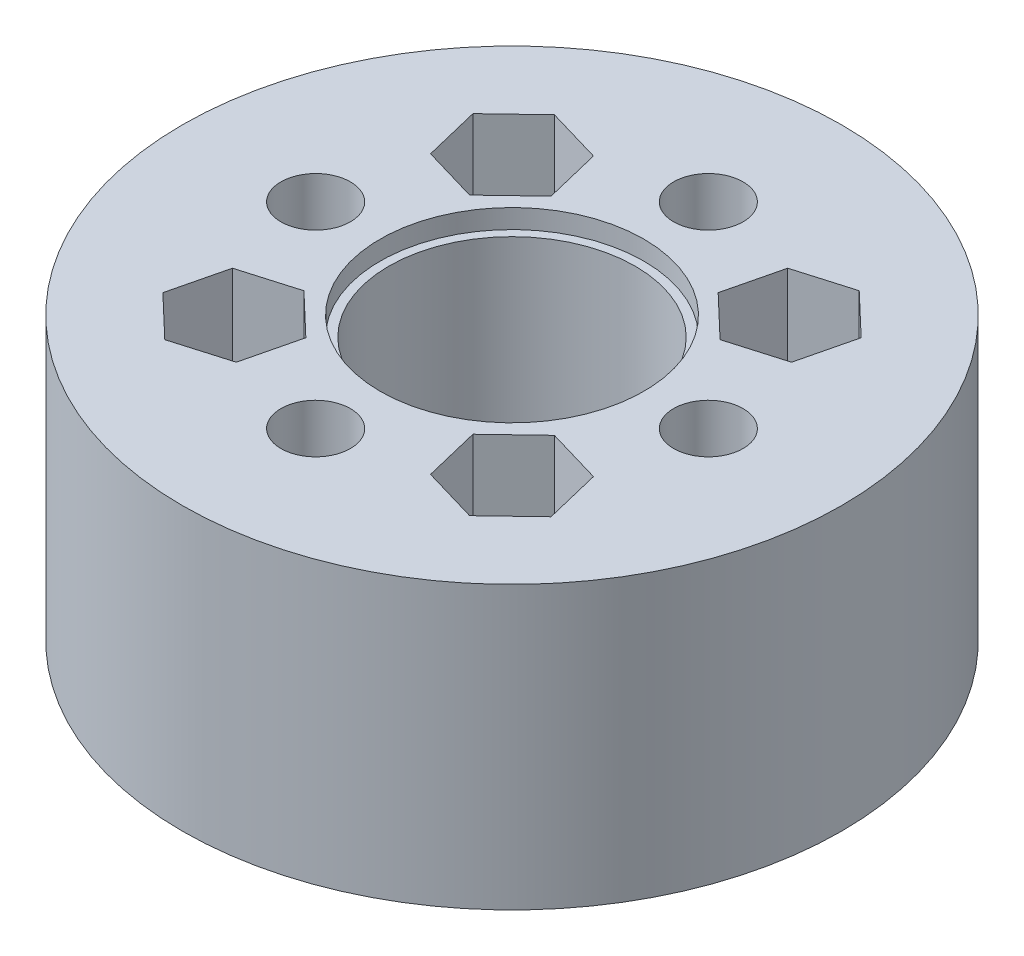
SolidWorks part; units mm, degrees
ref_plane "Front Plane" through (0, 0, 0) normal (0, 0, 1) x (1, 0, 0)
ref_plane "Top Plane" through (0, 0, 0) normal (0, 1, 0) x (1, 0, 0)
ref_plane "Right Plane" through (0, 0, 0) normal (1, 0, 0) x (0, 0, -1)
sketch "Sketch1" plane through (0, 0, 0) normal (0, 1, 0) x (1, 0, 0)
  line L0 (0, 11.315) -> (0, -11.315) construction
  line L1 (-8, 8) -> (8, 8) construction
  line L2 (-8, 8) -> (-8, -8) construction
  line L3 (-8, -8) -> (8, -8) construction
  line L4 (8, 8) -> (8, -8) construction
  line L5 (-8, 8) -> (8, -8) construction
  line L6 (-8, -8) -> (8, 8) construction
  line L7 (-11.315, 0) -> (11.315, 0) construction
  circle A0 centre (0, 0) radius 19
  circle A1 centre (-8, 8) radius 2.1
  circle A2 centre (-8, -8) radius 2.1
  circle A3 centre (8, 8) radius 2.1
  circle A4 centre (8, -8) radius 2.1
  circle A5 centre (0, 0) radius 7.1
  circle A6 centre (0, 11.315) radius 2
  circle A7 centre (11.315, 0) radius 2
  circle A8 centre (0, -11.315) radius 2
  circle A9 centre (-11.315, 0) radius 2
  point P15 (0, 0)
  point P18 (0, 0)
  dimension "40" = 38
  dimension "D4" = 4.2
  dimension "D5" = 14.2
  dimension "D8" = 4
  dimension "D2" = 16
  dimension "D3" = 16
  dimension "D6" = 22.63
  dimension "D7" = 22.63
extrude "Boss-Extrude1" add sketch "Sketch1" along normal blind 16.25
sketch "Sketch2" plane through (0, 16.25, 0) normal (0, 1, 0) x (1, 0, 0)
  circle A0 centre (0, 0) radius 7.6
  dimension "D1" = 15.2
extrude "Cut-Extrude1" cut sketch "Sketch2" against normal blind 1.1
sketch "Sketch3" plane through (0, 0, 0) normal (0, -1, 0) x (1, 0, 0)
  circle A0 centre (0, 0) radius 7.75
  dimension "D1" = 15.5
extrude "Cut-Extrude2" cut sketch "Sketch3" against normal blind 1.05
sketch "Sketch4" plane through (0, 16.25, 0) normal (0, 1, 0) x (1, 0, 0)
  line L0 (0, 0) -> (0, 4.7739) construction
  line L1 (-7.2168, 4.7739) -> (-4.8146, 7.0652)
  line L2 (-4.8146, 7.0652) -> (-5.5977, 10.2913)
  line L3 (-5.5977, 10.2913) -> (-8.7832, 11.2261)
  line L4 (-8.7832, 11.2261) -> (-11.1854, 8.9348)
  line L5 (-11.1854, 8.9348) -> (-10.4023, 5.7087)
  line L6 (-10.4023, 5.7087) -> (-7.2168, 4.7739)
  line L7 (0, 0) -> (2.7211, 0) construction
  line L8 (-10.4023, -5.7087) -> (-7.2168, -4.7739)
  line L9 (-11.1854, -8.9348) -> (-10.4023, -5.7087)
  line L10 (-8.7832, -11.2261) -> (-11.1854, -8.9348)
  line L11 (-5.5977, -10.2913) -> (-8.7832, -11.2261)
  line L12 (-4.8146, -7.0652) -> (-5.5977, -10.2913)
  line L13 (-7.2168, -4.7739) -> (-4.8146, -7.0652)
  line L14 (-7.2168, 4.7739) -> (-4.8146, 7.0652)
  line L15 (-4.8146, 7.0652) -> (-5.5977, 10.2913)
  line L16 (-5.5977, 10.2913) -> (-8.7832, 11.2261)
  line L17 (-8.7832, 11.2261) -> (-11.1854, 8.9348)
  line L18 (-11.1854, 8.9348) -> (-10.4023, 5.7087)
  line L19 (-10.4023, 5.7087) -> (-7.2168, 4.7739)
  line L20 (-10.4023, -5.7087) -> (-7.2168, -4.7739)
  line L21 (-11.1854, -8.9348) -> (-10.4023, -5.7087)
  line L22 (-8.7832, -11.2261) -> (-11.1854, -8.9348)
  line L23 (-5.5977, -10.2913) -> (-8.7832, -11.2261)
  line L24 (-4.8146, -7.0652) -> (-5.5977, -10.2913)
  line L25 (-7.2168, -4.7739) -> (-4.8146, -7.0652)
  line L26 (-7.2168, 4.7739) -> (-4.8146, 7.0652)
  line L27 (-4.8146, 7.0652) -> (-5.5977, 10.2913)
  line L28 (-5.5977, 10.2913) -> (-8.7832, 11.2261)
  line L29 (-8.7832, 11.2261) -> (-11.1854, 8.9348)
  line L30 (-11.1854, 8.9348) -> (-10.4023, 5.7087)
  line L31 (-10.4023, 5.7087) -> (-7.2168, 4.7739)
  line L32 (-10.4023, -5.7087) -> (-7.2168, -4.7739)
  line L33 (-11.1854, -8.9348) -> (-10.4023, -5.7087)
  line L34 (-8.7832, -11.2261) -> (-11.1854, -8.9348)
  line L35 (-5.5977, -10.2913) -> (-8.7832, -11.2261)
  line L36 (-4.8146, -7.0652) -> (-5.5977, -10.2913)
  line L37 (-7.2168, -4.7739) -> (-4.8146, -7.0652)
  line L38 (-7.2168, 4.7739) -> (-4.8146, 7.0652)
  line L39 (-4.8146, 7.0652) -> (-5.5977, 10.2913)
  line L40 (-5.5977, 10.2913) -> (-8.7832, 11.2261)
  line L41 (-8.7832, 11.2261) -> (-11.1854, 8.9348)
  line L42 (-11.1854, 8.9348) -> (-10.4023, 5.7087)
  line L43 (-10.4023, 5.7087) -> (-7.2168, 4.7739)
  line L44 (-10.4023, -5.7087) -> (-7.2168, -4.7739)
  line L45 (-11.1854, -8.9348) -> (-10.4023, -5.7087)
  line L46 (-8.7832, -11.2261) -> (-11.1854, -8.9348)
  line L47 (-5.5977, -10.2913) -> (-8.7832, -11.2261)
  line L48 (-4.8146, -7.0652) -> (-5.5977, -10.2913)
  line L49 (-7.2168, -4.7739) -> (-4.8146, -7.0652)
  line L50 (7.2168, -4.7739) -> (4.8146, -7.0652)
  line L51 (4.8146, -7.0652) -> (5.5977, -10.2913)
  line L52 (5.5977, -10.2913) -> (8.7832, -11.2261)
  line L53 (8.7832, -11.2261) -> (11.1854, -8.9348)
  line L54 (11.1854, -8.9348) -> (10.4023, -5.7087)
  line L55 (10.4023, -5.7087) -> (7.2168, -4.7739)
  line L56 (10.4023, 5.7087) -> (7.2168, 4.7739)
  line L57 (11.1854, 8.9348) -> (10.4023, 5.7087)
  line L58 (8.7832, 11.2261) -> (11.1854, 8.9348)
  line L59 (5.5977, 10.2913) -> (8.7832, 11.2261)
  line L60 (4.8146, 7.0652) -> (5.5977, 10.2913)
  line L61 (7.2168, 4.7739) -> (4.8146, 7.0652)
  line L62 (7.2168, -4.7739) -> (4.8146, -7.0652)
  line L63 (4.8146, -7.0652) -> (5.5977, -10.2913)
  line L64 (5.5977, -10.2913) -> (8.7832, -11.2261)
  line L65 (8.7832, -11.2261) -> (11.1854, -8.9348)
  line L66 (11.1854, -8.9348) -> (10.4023, -5.7087)
  line L67 (10.4023, -5.7087) -> (7.2168, -4.7739)
  line L68 (10.4023, 5.7087) -> (7.2168, 4.7739)
  line L69 (11.1854, 8.9348) -> (10.4023, 5.7087)
  line L70 (8.7832, 11.2261) -> (11.1854, 8.9348)
  line L71 (5.5977, 10.2913) -> (8.7832, 11.2261)
  line L72 (4.8146, 7.0652) -> (5.5977, 10.2913)
  line L73 (7.2168, 4.7739) -> (4.8146, 7.0652)
  line L74 (7.2168, -4.7739) -> (4.8146, -7.0652)
  line L75 (4.8146, -7.0652) -> (5.5977, -10.2913)
  line L76 (5.5977, -10.2913) -> (8.7832, -11.2261)
  line L77 (8.7832, -11.2261) -> (11.1854, -8.9348)
  line L78 (11.1854, -8.9348) -> (10.4023, -5.7087)
  line L79 (10.4023, -5.7087) -> (7.2168, -4.7739)
  line L80 (10.4023, 5.7087) -> (7.2168, 4.7739)
  line L81 (11.1854, 8.9348) -> (10.4023, 5.7087)
  line L82 (8.7832, 11.2261) -> (11.1854, 8.9348)
  line L83 (5.5977, 10.2913) -> (8.7832, 11.2261)
  line L84 (4.8146, 7.0652) -> (5.5977, 10.2913)
  line L85 (7.2168, 4.7739) -> (4.8146, 7.0652)
  line L86 (7.2168, -4.7739) -> (4.8146, -7.0652)
  line L87 (4.8146, -7.0652) -> (5.5977, -10.2913)
  line L88 (5.5977, -10.2913) -> (8.7832, -11.2261)
  line L89 (8.7832, -11.2261) -> (11.1854, -8.9348)
  line L90 (11.1854, -8.9348) -> (10.4023, -5.7087)
  line L91 (10.4023, -5.7087) -> (7.2168, -4.7739)
  line L92 (10.4023, 5.7087) -> (7.2168, 4.7739)
  line L93 (11.1854, 8.9348) -> (10.4023, 5.7087)
  line L94 (8.7832, 11.2261) -> (11.1854, 8.9348)
  line L95 (5.5977, 10.2913) -> (8.7832, 11.2261)
  line L96 (4.8146, 7.0652) -> (5.5977, 10.2913)
  line L97 (7.2168, 4.7739) -> (4.8146, 7.0652)
  circle A4 centre (-8, 8) radius 2.875 construction
  circle A5 centre (-8, -8) radius 2.875 construction
  circle A6 centre (-8, 8) radius 2.875 construction
  circle A7 centre (-8, -8) radius 2.875 construction
  circle A8 centre (-8, 8) radius 2.875 construction
  circle A9 centre (-8, -8) radius 2.875 construction
  circle A10 centre (-8, 8) radius 2.875 construction
  circle A11 centre (-8, -8) radius 2.875 construction
  circle A12 centre (8, -8) radius 2.875 construction
  circle A13 centre (8, 8) radius 2.875 construction
  circle A14 centre (8, -8) radius 2.875 construction
  circle A15 centre (8, 8) radius 2.875 construction
  circle A16 centre (8, -8) radius 2.875 construction
  circle A17 centre (8, 8) radius 2.875 construction
  circle A18 centre (8, -8) radius 2.875 construction
  circle A19 centre (8, 8) radius 2.875 construction
  circle M7 centre (8, -8) radius 2.1
  circle M8 centre (-8, -8) radius 2.1
  circle M10 centre (-8, 8) radius 2.1
  circle M11 centre (8, 8) radius 2.1
  dimension "D1" = 5.75
extrude "Cut-Extrude3" cut sketch "Sketch4" against normal blind 5 contours L5 L6 L1 L2 L3 L4 M10 | L61 L56 L57 L58 L59 L60 M11 | L13 L8 L9 L10 L11 L12 M8 | L54 L55 L50 L51 L52 L53 M7
